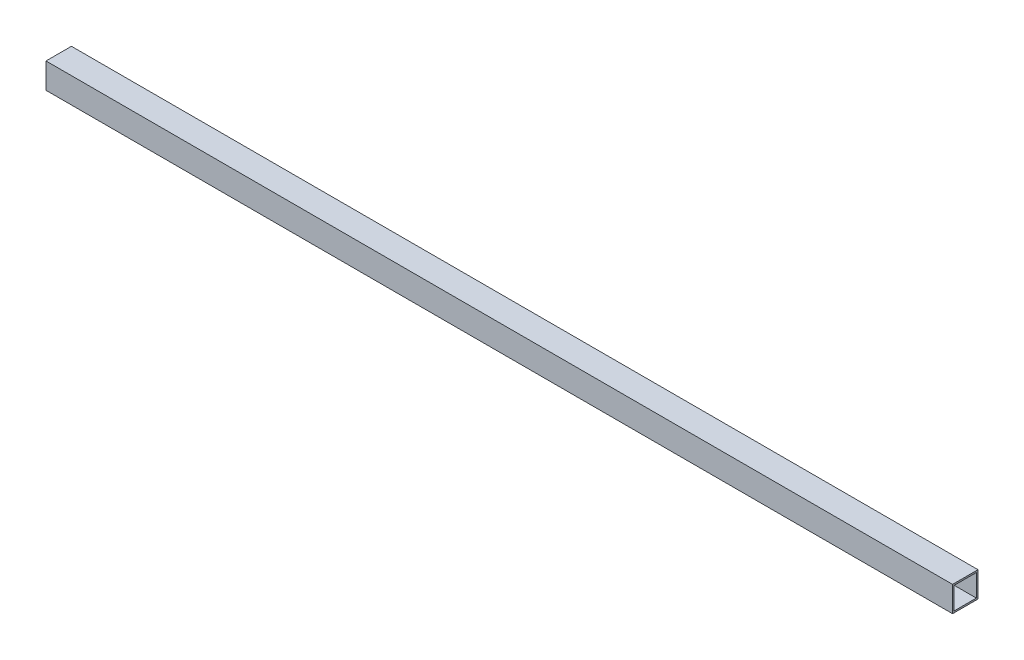
SolidWorks part; units mm, degrees
ref_plane "Front Plane" through (0, 0, 0) normal (0, 0, 1) x (1, 0, 0)
ref_plane "Top Plane" through (0, 0, 0) normal (0, 1, 0) x (1, 0, 0)
ref_plane "Right Plane" through (0, 0, 0) normal (1, 0, 0) x (0, 0, -1)
sketch "Sketch1" plane through (0, 0, 0) normal (0, 0, 1) x (1, 0, 0)
  line L0 (0, 0) -> (905.4, 0)
  dimension "D1" = 905.4
other "Al tube square AL TUBE 1 SQR X 0.065 WALL(1)"
ref_plane "Plane1" through (0, 0, 0) normal (1, 0, 0) x (0, 1, 0)
sketch "Sketch13" plane through (0, 0, 0) normal (1, 0, 0) x (0, 1, 0)
  line L0 (-11.049, -11.049) -> (-11.049, 11.049)
  line L1 (11.049, 11.049) -> (-11.049, 11.049)
  line L2 (11.049, 11.049) -> (11.049, -11.049)
  line L3 (-11.049, -11.049) -> (11.049, -11.049)
  line L4 (-12.7, -12.7) -> (12.7, -12.7)
  line L5 (-12.7, -12.7) -> (-12.7, 12.7)
  line L6 (12.7, 12.7) -> (-12.7, 12.7)
  line L7 (12.7, 12.7) -> (12.7, -12.7)
  line L8 (0, -11.049) -> (0, -12.7) construction
  line L9 (0, -11.049) -> (0, 11.049) construction
  line L10 (0, 11.049) -> (0, 12.7) construction
  line L11 (12.7, 0) -> (11.049, 0) construction
  line L12 (11.049, 0) -> (-11.049, 0) construction
  line L13 (-11.049, 0) -> (-12.7, 0) construction
  point P14 (0, 0)
  point P17 (0, 0)
  dimension "Thickness" = 1.651
  dimension "V_leg" = 25.4
  dimension "H_leg" = 25.4
